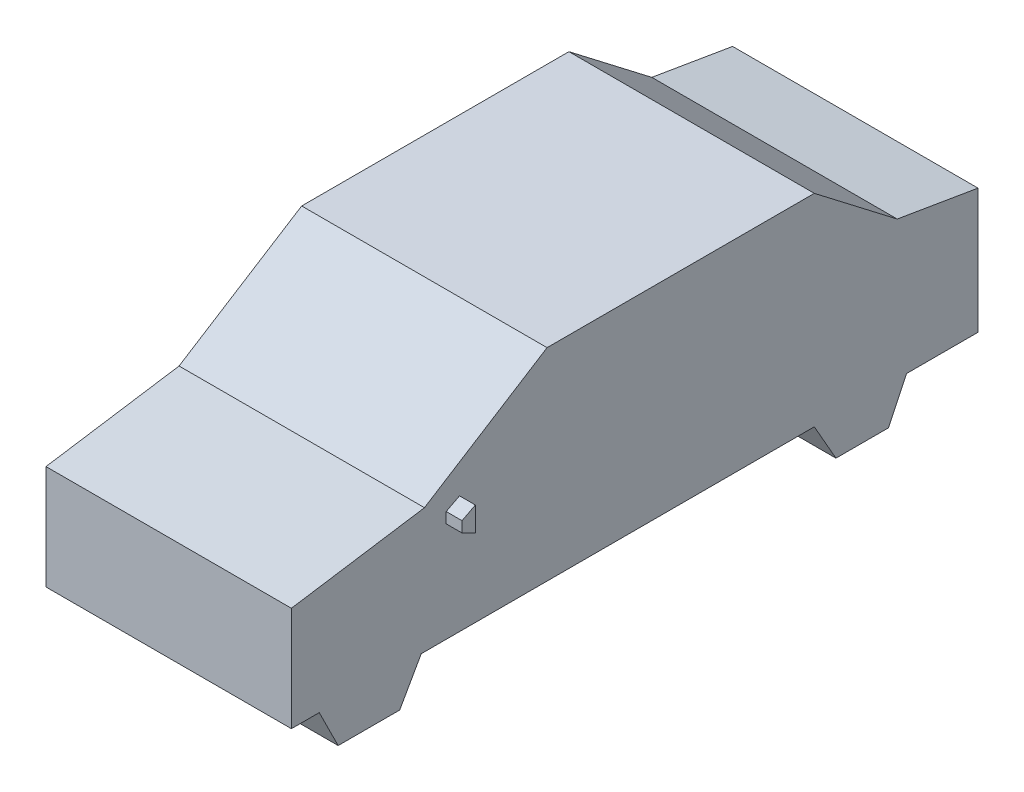
SolidWorks part; units mm, degrees
ref_plane "Спереди" through (0, 0, 0) normal (0, 0, 1) x (1, 0, 0)
ref_plane "Сверху" through (0, 0, 0) normal (0, 1, 0) x (1, 0, 0)
ref_plane "Справа" through (0, 0, 0) normal (1, 0, 0) x (0, 0, -1)
sketch "Эскиз1" plane through (0, 0, 0) normal (1, 0, 0) x (0, 0, -1)
  line L0 (0, 0) -> (0, 658.8756)
  line L1 (295.3794, -240) -> (684.0472, -240)
  line L2 (684.0472, -240) -> (820.1193, 0)
  line L3 (820.1193, 0) -> (3302.7851, 0)
  line L4 (3302.7851, 0) -> (3439.4534, -240)
  line L5 (4336.6377, 788.7348) -> (4336.6377, 0)
  line L6 (3439.4534, -240) -> (3771.2467, -240)
  line L7 (3771.2467, -240) -> (3886.0575, 0)
  line L8 (3886.0575, 0) -> (4336.6377, 0)
  line L9 (0, 658.8756) -> (840.4418, 788.7314)
  line L10 (840.4418, 788.7314) -> (1614.7932, 1277)
  line L11 (1614.7932, 1277) -> (3302.7851, 1277)
  line L12 (3302.7851, 1277) -> (3826.4721, 874.6592)
  line L13 (295.3794, -240) -> (176.0173, 0)
  line L14 (176.0173, 0) -> (0, 0)
  line L15 (3826.4721, 874.6592) -> (4336.6377, 788.7348)
extrude "Бобышка-Вытянуть1" add sketch "Эскиз1" along normal blind 1550
sketch "Эскиз2" plane through (1550, 0, 0) normal (1, 0, 0) x (0, 0, -1)
  line L0 (977.68, 699.1362) -> (977.68, 631.78)
  line L1 (977.68, 631.78) -> (1061.8853, 590.6456)
  line L2 (1061.8853, 590.6456) -> (1061.8853, 742.845)
  line L3 (1061.8853, 742.845) -> (977.68, 699.1362)
extrude "Бобышка-Вытянуть2" add sketch "Эскиз2" against normal blind 1650 and the other way blind 100
